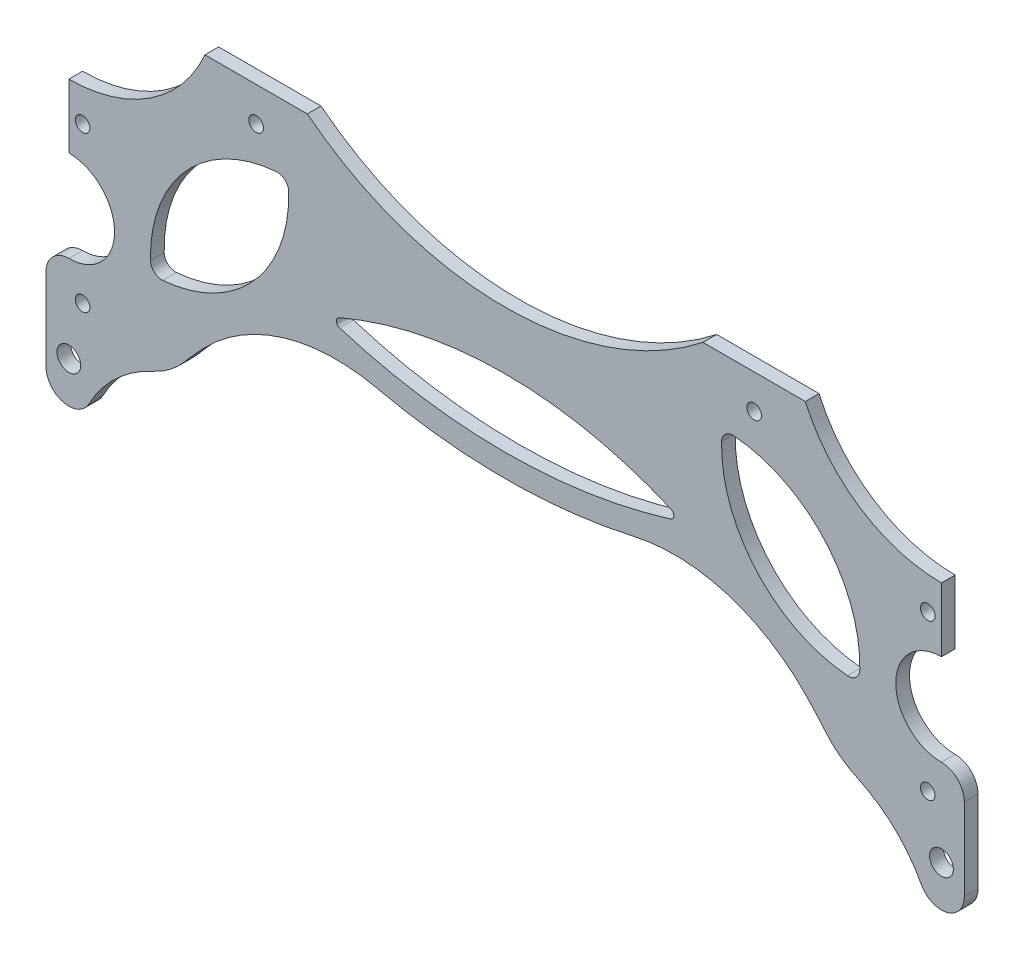
SolidWorks part; units mm, degrees
material "Thornel Mat VMA"
ref_plane "前视基准面" through (0, 0, 0) normal (0, 0, 1) x (1, 0, 0)
ref_plane "上视基准面" through (0, 0, 0) normal (0, 1, 0) x (1, 0, 0)
ref_plane "右视基准面" through (0, 0, 0) normal (1, 0, 0) x (0, 0, -1)
sketch "草图1" plane through (0, 0, 0) normal (0, 0, 1) x (1, 0, 0)
  line L0 (-95.5, -8.75) -> (95.5, -8.75) construction
  line L1 (-95.5, -33.75) -> (95.5, -33.75) construction
  line L2 (-95.5, -33.75) -> (-95.5, 33.75) construction
  line L3 (-95.5, 33.75) -> (95.5, 33.75) construction
  line L4 (95.5, -33.75) -> (95.5, 33.75) construction
  line L5 (-95.5, -33.75) -> (95.5, 33.75) construction
  line L6 (-95.5, 33.75) -> (95.5, -33.75) construction
  line L7 (-50, -8.75) -> (-50, -33.75) construction
  line L8 (50, -8.75) -> (50, -33.75) construction
  line L9 (-43.3013, 33.75) -> (-65.7133, 33.75)
  line L10 (-95.5, 14.25) -> (-95.5, 0.25)
  line L11 (-95.5, -19.75) -> (-95.5, -33.75)
  line L12 (-95.5, -33.75) -> (-75.5, -33.75)
  line L13 (0, 0) -> (0, -75.6259) construction
  line L14 (43.3013, 33.75) -> (65.7133, 33.75)
  line L15 (95.5, 14.25) -> (95.5, 0.25)
  line L16 (95.5, -19.75) -> (95.5, -33.75)
  line L17 (95.5, -33.75) -> (75.5, -33.75)
  circle A0 centre (0, -85.255) radius 91.3948 construction
  arc A1 (-75.5, -33.75) -> (75.5, -33.75) centre (0, -85.255) cw
  circle A2 centre (-95.5, -9.75) radius 10 construction
  circle A3 centre (-95.5, 46.75) radius 32.5 construction
  arc A4 (-95.5, -19.75) -> (-95.5, 0.25) centre (-95.5, -9.75) ccw
  arc A5 (-95.5, 14.25) -> (-65.7133, 33.75) centre (-95.5, 46.75) ccw
  arc A6 (95.5, -19.75) -> (95.5, 0.25) centre (95.5, -9.75) cw
  arc A7 (95.5, 14.25) -> (65.7133, 33.75) centre (95.5, 46.75) cw
  arc A8 (-43.3013, 33.75) -> (43.3013, 33.75) centre (0, 88.75) ccw
  point P0 (0, 0)
  point P12 (-75.5, -33.75)
  point P13 (75.5, -33.75)
  point P18 (-95.5, -9.75)
  point P21 (-95.5, 14.25)
  dimension "D8" = 24
  dimension "D9" = 20
  dimension "D11" = 65
  dimension "D12" = 140
  dimension "D1" = 67.5
  dimension "D2" = 191
  dimension "D3" = 25
  dimension "D4" = 50
  dimension "D5" = 50
  dimension "D6" = 20
  dimension "D7" = 20
  dimension "D10" = 48
  dimension "D13" = 55
extrude "凸台-拉伸1" add sketch "草图1" along normal blind 3 contours A8 L9 A5 L10 A4 L11 L12 A1 L17 L16 A6 L15 A7 L14
sketch "草图2" plane through (0, 0, 3) normal (0, 0, 1) x (1, 0, 0)
  line L0 (-43.3013, 33.75) -> (43.3013, 33.75) construction
  line L1 (0, 33.75) -> (0, -10.6023) construction
  line L2 (0, 33.75) -> (0, 113.75) construction
  circle A0 centre (0, 113.75) radius 125 construction
  arc A1 (-71.6448, 11.3194) -> (73.2747, 12.479) centre (0, 113.75) ccw
  dimension "D2" = 250
  dimension "D1" = 80
extrude "拉伸-薄壁1" add sketch "草图2" against normal up to surface (3 mm away) thin up to face at (0, 0.3934, 0) thin type mid plane wall 5
fillet "圆角1" radius 40 2 edges at (44.8284, -5.6094, 1.5) (-44.8284, -5.6094, 1.5)
sketch "草图3" plane through (0, 0, 3) normal (0, 0, 1) x (1, 0, 0)
  line L0 (-95.5, -33.75) -> (-29.5046, 39.5453) construction
  line L1 (-95.5, -33.75) -> (-75.5, -33.75) construction
  line L2 (0, 0) -> (0, 54.1854) construction
  line L3 (-62.5023, 2.8976) -> (-95.5, 32.6089) construction
  arc A0 (-77.4645, -13.7196) -> (-47.5401, 19.5149) centre (-77.3652, 16.2803) ccw
  arc A1 (-77.4645, -13.7196) -> (-47.5401, 19.5149) centre (-47.6394, -10.485) cw
  arc A2 (77.4645, -13.7196) -> (47.5401, 19.5149) centre (47.6394, -10.485) ccw
  arc A3 (77.4645, -13.7196) -> (47.5401, 19.5149) centre (77.3652, 16.2803) cw
  dimension "D2" = 60
  dimension "D1" = 20
  dimension "D3" = 98.6285
  dimension "D4" = 48
extrude "切除-拉伸1" cut sketch "草图3" against normal up to next
fillet "圆角2" radius 20 2 edges at (75.5, -33.75, 1.5) (-75.5, -33.75, 1.5)
sketch "草图4" plane through (0, 0, 3) normal (0, 0, 1) x (1, 0, 0)
  line L0 (-92.5, -33.75) -> (-92.5, -26.75) construction
  line L1 (-95.5, -33.75) -> (-85.4157, -33.75) construction
  line L2 (-95.5, -19.75) -> (-95.5, -33.75) construction
  line L3 (-92.5, -26.75) -> (-92.5, 7.25) construction
  line L5 (0, 0) -> (0, -52.8103) construction
  line L6 (92.5, -26.75) -> (92.5, 7.25) construction
  line L7 (92.5, -33.75) -> (92.5, -26.75) construction
  circle A0 centre (-92.5, -26.75) radius 1.6
  circle A1 centre (-92.5, 7.25) radius 1.6
  circle A2 centre (92.5, 7.25) radius 1.6
  circle A3 centre (92.5, -26.75) radius 1.6
  dimension "D3" = 3.2
  dimension "D5" = 3.2
  dimension "D1" = 3
  dimension "D2" = 7
  dimension "D4" = 34
extrude "切除-拉伸2" cut sketch "草图4" against normal up to next
sketch "草图5" plane through (0, 0, 3) normal (0, 0, 1) x (1, 0, 0)
  line L0 (-54.5073, 33.75) -> (-54.5073, 26.25) construction
  line L1 (-43.3013, 33.75) -> (-65.7133, 33.75) construction
  line L2 (0, 0) -> (0, 26.25) construction
  circle A0 centre (-54.5073, 26.25) radius 1.6
  circle A1 centre (54.5073, 26.25) radius 1.6
  dimension "D2" = 3.2
  dimension "D1" = 7.5
extrude "切除-拉伸3" cut sketch "草图5" against normal up to next
fillet "圆角3" radius 1 2 edges at (38.7228, -2.4688, 1.5) (-38.7228, -2.4688, 1.5)
sketch "草图6" plane through (0, 0, 3) normal (0, 0, 1) x (1, 0, 0)
  line L0 (-95.5, -24.75) -> (-95.5, -42.75) construction
  line L1 (-90.5, -24.75) -> (-90.5, -42.75)
  line L2 (-100.5, -24.75) -> (-100.5, -42.75)
  line L3 (0, 0) -> (0, -67.3999) construction
  line L4 (95.5, -24.75) -> (95.5, -42.75) construction
  line L5 (90.5, -24.75) -> (90.5, -42.75)
  line L6 (100.5, -24.75) -> (100.5, -42.75)
  arc A0 (-90.5, -24.75) -> (-100.5, -24.75) centre (-95.5, -24.75) ccw
  arc A1 (-100.5, -42.75) -> (-90.5, -42.75) centre (-95.5, -42.75) ccw
  circle A2 centre (-92.5, -26.75) radius 1.6
  circle A5 centre (92.5, -26.75) radius 1.6
  arc A6 (90.5, -24.75) -> (100.5, -24.75) centre (95.5, -24.75) cw
  arc A7 (100.5, -42.75) -> (90.5, -42.75) centre (95.5, -42.75) cw
  circle A8 centre (-95.5, -38.75) radius 2.6
  circle A9 centre (95.5, -38.75) radius 2.6
  point P2 (-95.5, -33.75)
  point P18 (95.5, -33.75)
  dimension "D1" = 3.2
  dimension "D2" = 5.2
  dimension "D3" = 5
extrude "凸台-拉伸2" add sketch "草图6" against normal up to surface (3 mm away) up to face at (56.1073, 26.25, 0)
fillet "圆角4" radius 30 2 edges at (90.5, -33.75, 1.5) (-90.5, -33.75, 1.5)
fillet "圆角5" radius 2.5 4 edges at (-77.4645, -13.7196, 1.5) (-47.5401, 19.5149, 1.5) (77.4645, -13.7196, 1.5) (47.5401, 19.5149, 1.5)
